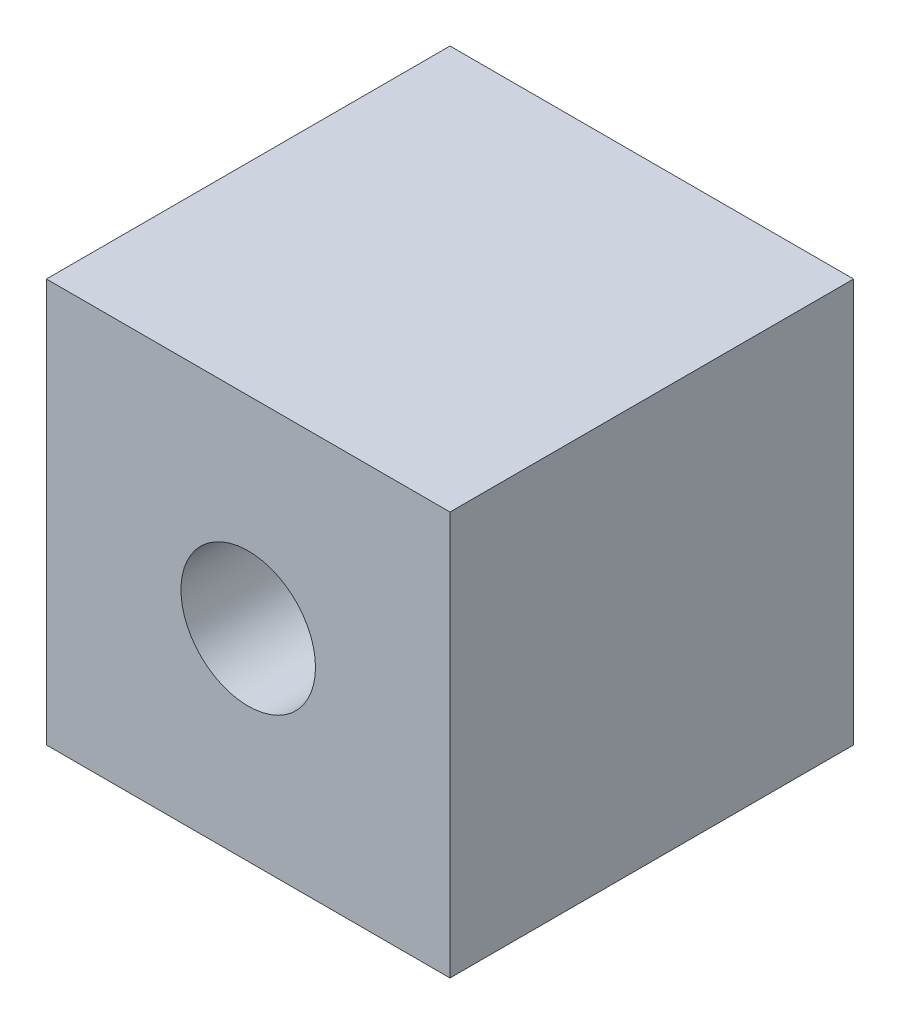
SolidWorks part; units mm, degrees
material "Oak"
ref_plane "Front Plane" through (0, 0, 0) normal (0, 0, 1) x (1, 0, 0)
ref_plane "Top Plane" through (0, 0, 0) normal (0, 1, 0) x (1, 0, 0)
ref_plane "Right Plane" through (0, 0, 0) normal (1, 0, 0) x (0, 0, -1)
sketch "Sketch1" plane through (0, 0, 0) normal (0, 0, 1) x (1, 0, 0)
  line L1 (-38.1, -38.1) -> (38.1, -38.1)
  line L2 (-38.1, -38.1) -> (-38.1, 38.1)
  line L3 (-38.1, 38.1) -> (38.1, 38.1)
  line L4 (38.1, -38.1) -> (38.1, 38.1)
  line L5 (-38.1, -38.1) -> (38.1, 38.1) construction
  line L6 (-38.1, 38.1) -> (38.1, -38.1) construction
  point P0 (0, 0)
  dimension "D1" = 76.2
  dimension "D2" = 76.2
extrude "Boss-Extrude1" add sketch "Sketch1" along normal blind 76.2
sketch "Sketch2" plane through (0, 0, 76.2) normal (0, 0, 1) x (1, 0, 0)
  circle A0 centre (0, 0) radius 12.7
  dimension "D1" = 25.4
extrude "Cut-Extrude1" cut sketch "Sketch2" against normal blind 25.4
